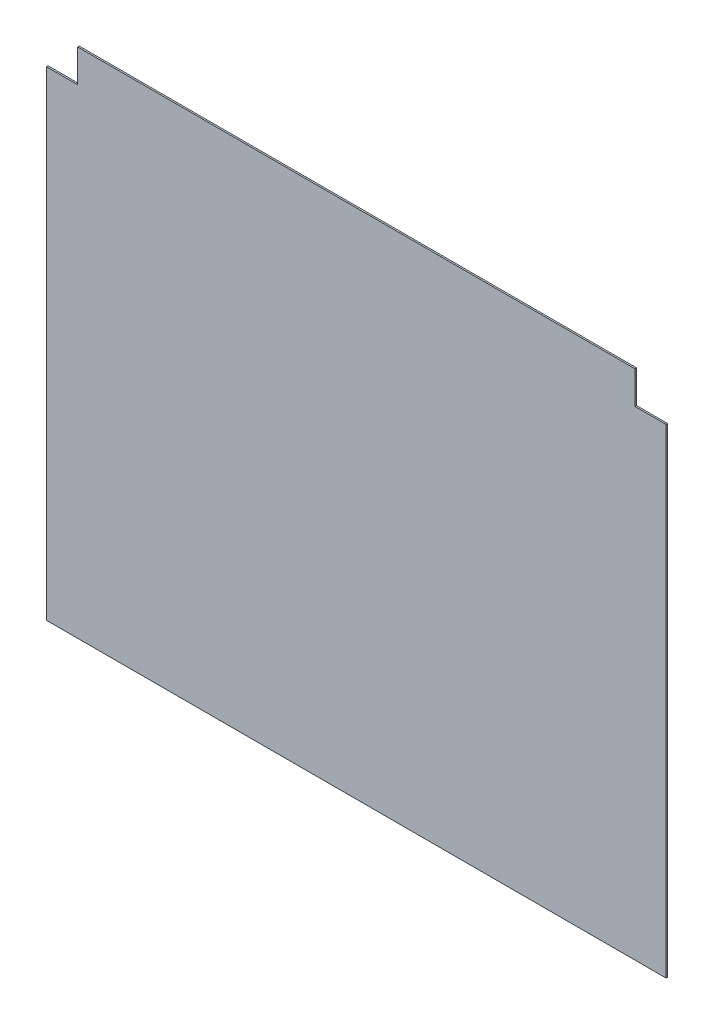
SolidWorks part; units mm, degrees
material "3.0205 (EN-AW 1200)"
ref_plane "정면" through (0, 0, 0) normal (0, 0, 1) x (1, 0, 0)
ref_plane "윗면" through (0, 0, 0) normal (0, 1, 0) x (1, 0, 0)
ref_plane "우측면" through (0, 0, 0) normal (1, 0, 0) x (0, 0, -1)
sketch "스케치1" plane through (0, 0, 0) normal (0, 0, 1) x (1, 0, 0)
  line L0 (0, 0) -> (398, 0)
  line L1 (398, 0) -> (398, 308)
  line L2 (398, 308) -> (378, 308)
  line L3 (378, 308) -> (378, 329)
  line L4 (378, 329) -> (20, 329)
  line L5 (20, 329) -> (20, 308)
  line L6 (20, 308) -> (0, 308)
  line L7 (0, 308) -> (0, 0)
  dimension "D1" = 358
  dimension "D2" = 308
  dimension "D3" = 21
  dimension "D4" = 20
  dimension "D5" = 21
  dimension "D6" = 20
extrude "보스-돌출1" add sketch "스케치1" along normal blind 1 contours L4 L5 L6 L7 L0 L1 L2 L3
